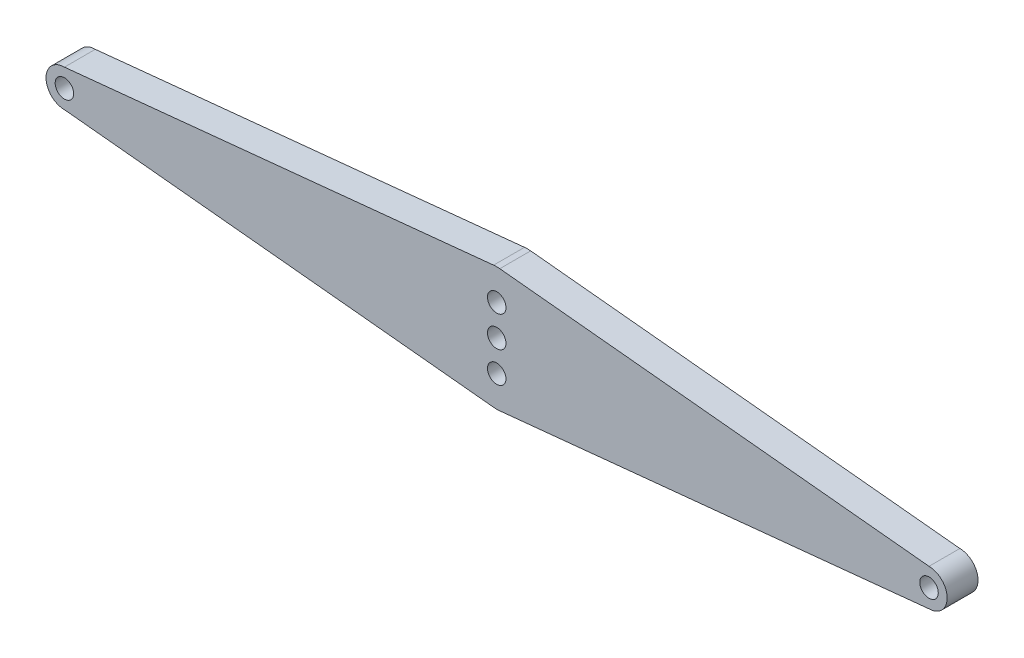
SolidWorks part; units mm, degrees
ref_plane "前视基准面" through (0, 0, 0) normal (0, 0, 1) x (1, 0, 0)
ref_plane "上视基准面" through (0, 0, 0) normal (0, 1, 0) x (1, 0, 0)
ref_plane "右视基准面" through (0, 0, 0) normal (1, 0, 0) x (0, 0, -1)
sketch "草图1" plane through (0, 0, 0) normal (0, 0, 1) x (1, 0, 0)
  line L0 (-14.0068, 0) -> (14.0068, 0)
  line L1 (0, 1) -> (0, -1)
  line L2 (-14.0068, 0.5972) -> (-0.1, 1.995)
  line L3 (14.0068, 0.5972) -> (0.1, 1.995)
  line L4 (14.0068, -0.5972) -> (0.1, -1.995)
  line L5 (-14.0068, -0.5972) -> (-0.1, -1.995)
  circle A0 centre (0, 1) radius 0.3
  circle A1 centre (0, -1) radius 0.3
  circle A2 centre (-14.0068, 0) radius 0.3
  circle A3 centre (14.0068, 0) radius 0.3
  circle A4 centre (-14.0068, 0) radius 0.5972
  circle A5 centre (0, 1) radius 1
  circle A6 centre (0, -1) radius 1
  circle A7 centre (13.9979, 0) radius 0.5972
  circle A8 centre (0, 0) radius 0.3
extrude "凸台-拉伸4" add sketch "草图1" along normal blind 1
